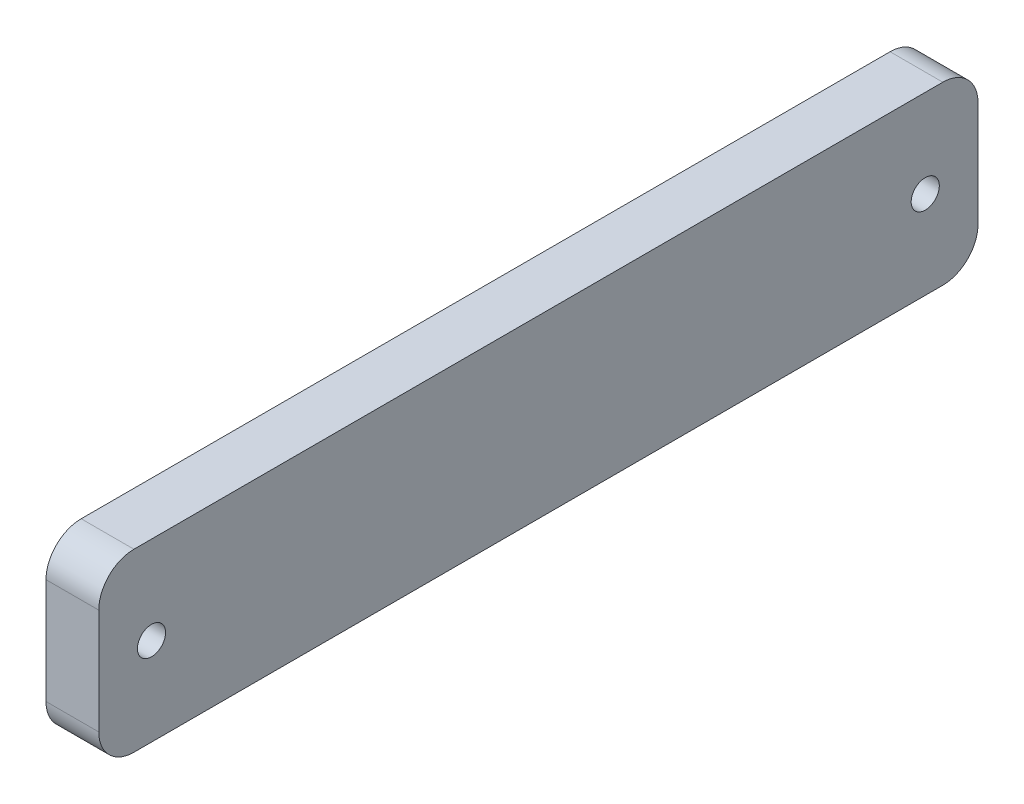
SolidWorks part; units mm, degrees
material "Teca"
ref_plane "Front Plane" through (0, 0, 0) normal (0, 0, 1) x (1, 0, 0)
ref_plane "Top Plane" through (0, 0, 0) normal (0, 1, 0) x (1, 0, 0)
ref_plane "Right Plane" through (0, 0, 0) normal (1, 0, 0) x (0, 0, -1)
sketch "Esboço1" plane through (0, 0, 0) normal (1, 0, 0) x (0, 0, -1)
  line L1 (-25, 5) -> (25, 5)
  line L2 (-25, 5) -> (-25, -5)
  line L3 (-25, -5) -> (25, -5)
  line L4 (25, 5) -> (25, -5)
  line L5 (0, -5) -> (0, 5) construction
  line L6 (-25, 0) -> (25, 0) construction
  circle A0 centre (-22, 0) radius 0.8
  circle A1 centre (22, 0) radius 0.8
  point P0 (0, 0)
  dimension "D3" = 1.6
  dimension "D1" = 10
  dimension "D2" = 50
  dimension "D4" = 3
extrude "Ressalto-extrusão1" add sketch "Esboço1" along normal blind 3
fillet "Filete1" radius 2 4 edges at (1.5, -5, -25) (1.5, 5, -25) (1.5, -5, 25) (1.5, 5, 25)
